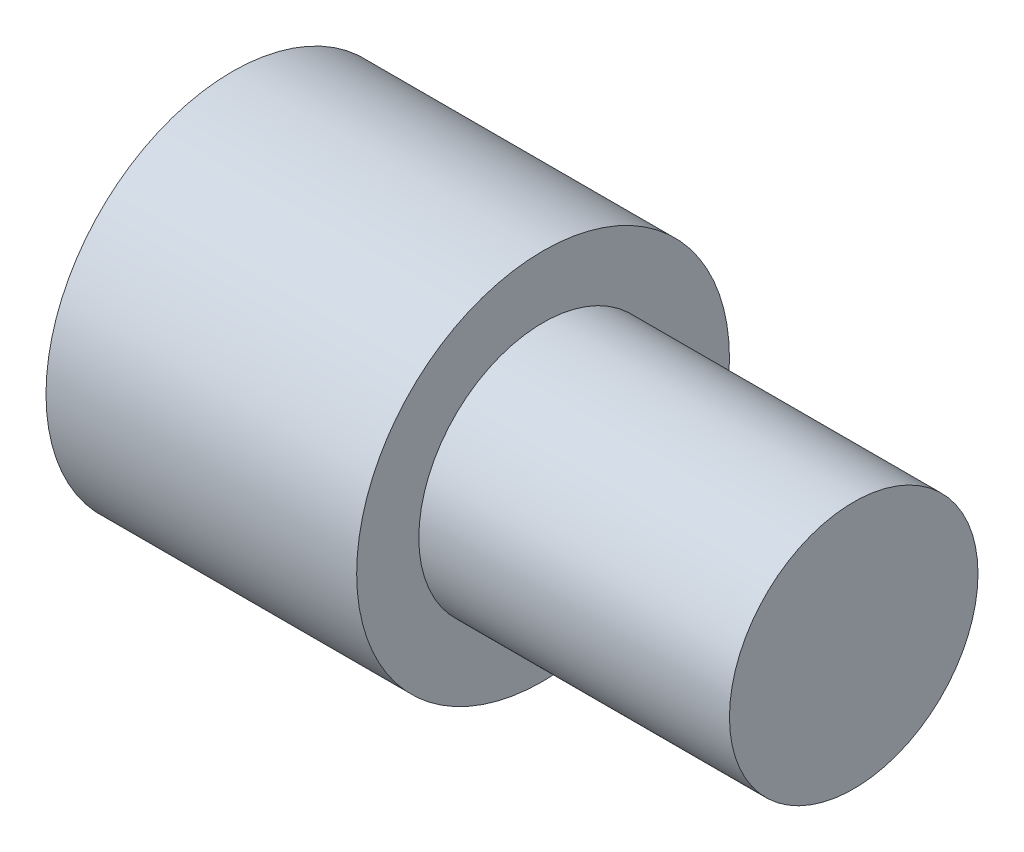
SolidWorks part; units mm, degrees
ref_plane "Front Plane" through (0, 0, 0) normal (0, 0, 1) x (1, 0, 0)
ref_plane "Top Plane" through (0, 0, 0) normal (0, 1, 0) x (1, 0, 0)
ref_plane "Right Plane" through (0, 0, 0) normal (1, 0, 0) x (0, 0, -1)
sketch "Sketch1" plane through (0, 0, 0) normal (1, 0, 0) x (0, 0, -1)
  circle A0 centre (0, 0) radius 4
  dimension "D1" = 8
extrude "Boss-Extrude1" add sketch "Sketch1" along normal blind 10
sketch "Sketch2" plane through (0, 0, 0) normal (-1, 0, 0) x (0, 0, 1)
  circle A0 centre (0, 0) radius 6
  dimension "D1" = 12
extrude "Boss-Extrude2" add sketch "Sketch2" along normal blind 10
